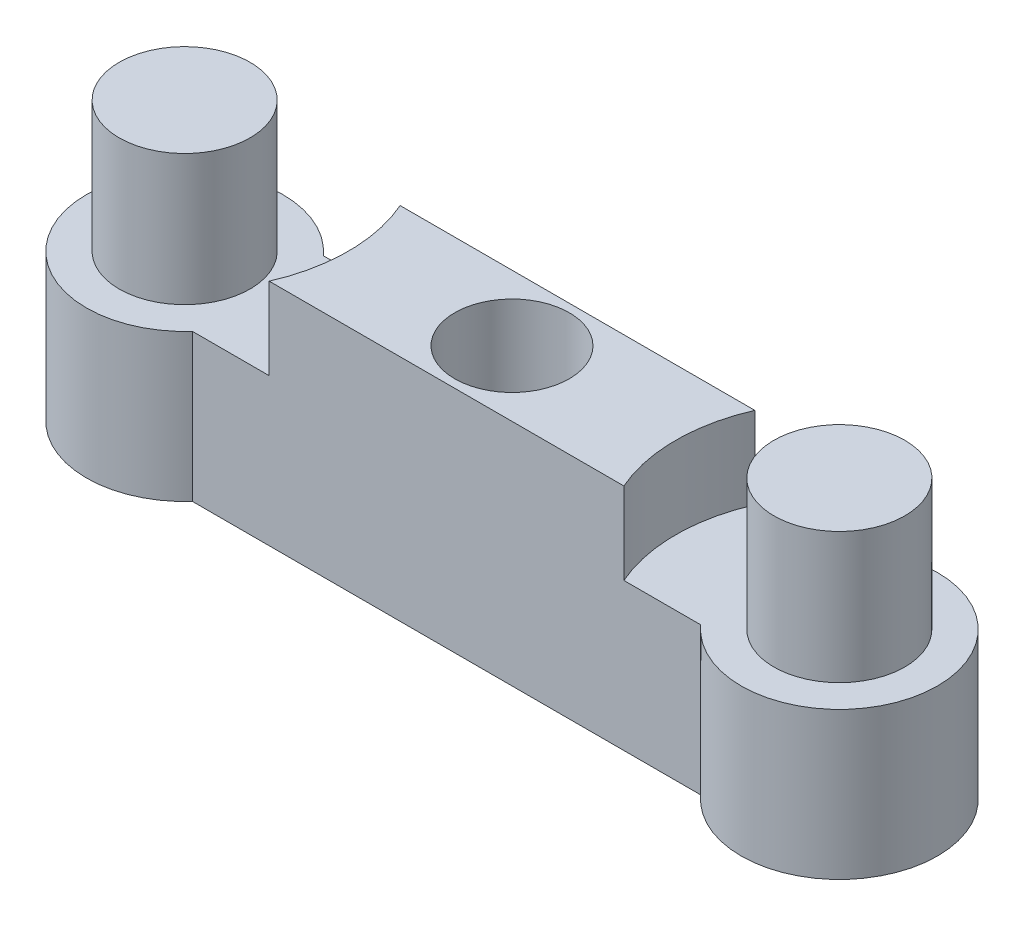
SolidWorks part; units mm, degrees
ref_plane "Front" through (0, 0, 0) normal (0, 0, 1) x (1, 0, 0)
ref_plane "Top" through (0, 0, 0) normal (0, 1, 0) x (1, 0, 0)
ref_plane "Right" through (0, 0, 0) normal (1, 0, 0) x (0, 0, -1)
sketch "草图1" plane through (0, 0, 0) normal (0, 1, 0) x (1, 0, 0)
  line L0 (0, 25.0119) -> (0, -20.6067) construction
  line L1 (-31.2771, 0) -> (37.836, 0) construction
  line L3 (7.7639, -2) -> (-7.7639, -2)
  line L5 (7.7639, 2) -> (-7.7639, 2)
  line L7 (7.7639, -2) -> (-7.7639, 2) construction
  line L8 (7.7639, 2) -> (-7.7639, -2) construction
  arc A0 (-7.7639, 2) -> (-7.7639, -2) centre (-10, 0) ccw
  arc A1 (7.7639, 2) -> (7.7639, -2) centre (10, 0) cw
  point P9 (0, 0)
  dimension "D2" = 6
  dimension "D1" = 4
  dimension "D3" = 10
extrude "凸台-拉伸1" add sketch "草图1" along normal blind 9
sketch "草图2" plane through (0, 9, 0) normal (0, 1, 0) x (1, 0, 0)
  line L0 (0, 19.2239) -> (0, -15.3802) construction
  circle A0 centre (-10, 0) radius 5
  circle A1 centre (10, 0) radius 5
  dimension "D1" = 10
extrude "切除-拉伸1" cut sketch "草图2" against normal blind 4.5
sketch "草图3" plane through (0, 4.5, 0) normal (0, 1, 0) x (1, 0, 0)
  line L0 (0, 14.6941) -> (0, -11.7424) construction
  circle A0 centre (-10, 0) radius 2
  circle A1 centre (10, 0) radius 2
  dimension "D1" = 4
extrude "凸台-拉伸2" add sketch "草图3" along normal blind 4
sketch "草图4" plane through (0, 9, 0) normal (0, 1, 0) x (1, 0, 0)
  circle A0 centre (0, 0) radius 1
  dimension "D1" = 2
extrude "切除-拉伸2" cut sketch "草图4" against normal through all
sketch "草图5" plane through (0, 9, 0) normal (0, 1, 0) x (1, 0, 0)
  circle A0 centre (0, 0) radius 1.75
  dimension "D1" = 3.5
extrude "切除-拉伸3" cut sketch "草图5" against normal blind 7
ref_plane "基准面1" through (0, 0, 0) normal (0, 1, 0) x (1, 0, 0)
sketch "草图6" plane through (0, 9, 0) normal (0, 1, 0) x (1, 0, 0)
  line L1 (6.3939, -3.2268) -> (-6.3939, -3.2268)
  line L2 (6.3939, -3.2268) -> (6.3939, 3.2268)
  line L3 (6.3939, 3.2268) -> (-6.3939, 3.2268)
  line L4 (-6.3939, -3.2268) -> (-6.3939, 3.2268)
  line L5 (6.3939, -3.2268) -> (-6.3939, 3.2268) construction
  line L6 (6.3939, 3.2268) -> (-6.3939, -3.2268) construction
  point P0 (0, 0)
extrude "切除-拉伸4" cut sketch "草图6" against normal blind 2
